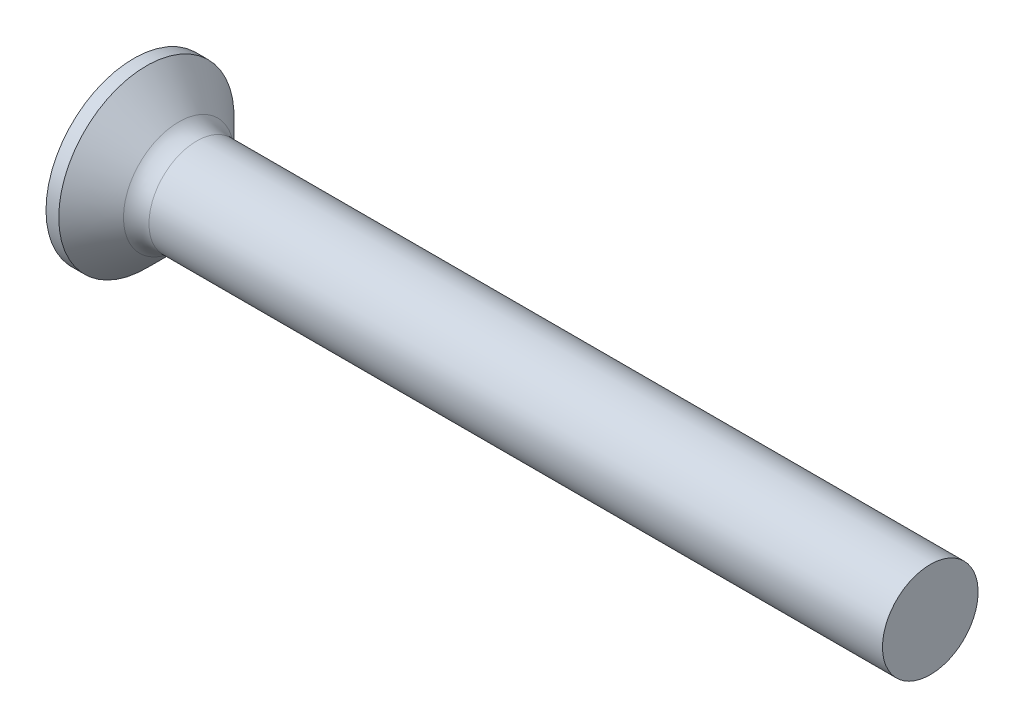
SolidWorks part; units mm, degrees
ref_plane "Plane1" through (0, 0, 0) normal (0, 0, 1) x (1, 0, 0)
ref_plane "Plane2" through (0, 0, 0) normal (0, 1, 0) x (1, 0, 0)
ref_plane "Plane3" through (0, 0, 0) normal (1, 0, 0) x (0, 0, -1)
sketch "BodySke" plane through (0, 0, 0) normal (0, 0, 1) x (1, 0, 0)
  line L0 (0, 0) -> (0, 2.75)
  line L1 (0, 2.75) -> (0.4, 2.75)
  line L2 (1.65, 1.5) -> (25, 1.5)
  line L3 (25, 1.5) -> (25, 0)
  line L4 (25, 0) -> (0, 0)
  line L5 (-6.35, 0) -> (82.55, 0) construction
  line L6 (1.65, -1.5) -> (25, -1.5) construction
  line L7 (0.4, -2.75) -> (1.65, -1.5) construction
  line L8 (0.4, 2.75) -> (1.65, 1.5)
  line L9 (0, -2.75) -> (0.4, -2.75) construction
  line L10 (2.15, 3.0875) -> (2.15, -6.4375) construction
  line L11 (0, 6.35) -> (0, -3.175) construction
  dimension "Diameter" = 3
  dimension "Length" = 25
  dimension "Head_ht" = 1.65
  dimension "Head_dia" = 5.5
  dimension "Head_ang" = 90
  dimension "D6" = 0.4
  dimension "Advance" = 0.5
  dimension "Thread_nom" = 25
revolve "Base-Revolve" add sketch "BodySke" angle 360 about L5
cosmetic thread "ThreadCosmetic" [suppressed] parameters "Thread_length"=22.85, "Thread_minor"=2.439
fillet "Fillet1" radius 0.8 1 edges at (1.65, 0, 1.5)
sketch "Sketch3" plane through (0, 0, 0) normal (-1, 0, 0) x (0, 0, 1)
  line L0 (-0.37, 1.5) -> (0.37, 1.5)
  line L1 (0.37, 1.5) -> (0.37, -1.5)
  line L2 (0.37, -1.5) -> (-0.37, -1.5)
  line L3 (-0.37, -1.5) -> (-0.37, 1.5)
  dimension "D1" = 1.5
  dimension "Cross_dia" = 3
  dimension "D2" = 0.37
  dimension "Cross_width" = 0.74
ref_plane "Plane4" through (2.01, 0, 0) normal (-1, 0, 0) x (0, 0, 1)
sketch "Sketch4" plane through (2.01, 0, 0) normal (-1, 0, 0) x (0, 0, 1)
  line L0 (-0.37, 0.4979) -> (0.37, 0.4979)
  line L3 (0.37, 0.4979) -> (0.37, -0.4979)
  line L4 (0.37, -0.4979) -> (-0.37, -0.4979)
  line L5 (-0.37, -0.4979) -> (-0.37, 0.4979)
  dimension "D1" = 0.74
  dimension "D2" = 0.9957
  dimension "D3" = 0.37
  dimension "D4" = 0.4979
loft "Recess" cut profiles "Sketch3", "Sketch4"
pattern_circular "RecPat" count 2 every 90 about axis through (0, 0, 0) along (1, 0, 0) of "Recess"
sketch "RecCorSke" plane through (0, 0, 0) normal (0, 0, 1) x (1, 0, 0)
  line L0 (-3.175, 0) -> (15.875, 0) construction
  line L2 (0, 0) -> (0, 0.6966)
  line L3 (0, 0.6966) -> (2.01, 0.556)
  line L4 (2.01, 0.556) -> (2.1907, 0)
  line L5 (2.1907, 0) -> (0, 0)
  dimension "Diameter" = 1.112
  dimension "Depth" = 2.01
  dimension "Draft_angle" = 4
  dimension "Bottom_angle" = 18
revolve "RecessCore" cut sketch "RecCorSke" angle 360 about L0
sketch "ThdSchSke" plane through (0, 0, 0) normal (0, 0, 1) x (1, 0, 0)
  line L0 (2.15, -1.2195) -> (1.9536, -1.5)
  line L1 (2.15, -1.2195) -> (2.3464, -1.5)
  line L2 (2.3464, -1.5) -> (2.3464, -1.875)
  line L3 (-3.175, 0) -> (5.1513, 0) construction
  line L5 (2.3464, -1.875) -> (1.9536, -1.875)
  line L6 (1.9536, -1.875) -> (1.9536, -1.5)
  line L7 (0, 2.75) -> (0, -2.75) construction
  dimension "Thread_minor" = 2.439
  dimension "Diameter" = 3
  dimension "Start" = 2.15
  dimension "SideAngle" = 55
  dimension "VeeAngle" = 70
  dimension "Overcut" = 3.75
revolve "ThreadSchematic" [suppressed] cut sketch "ThdSchSke" angle 360 about L3
pattern_linear "ThdSchPat" [suppressed]
equation "\"D1@Sketch3\" = \"Cross_dia@Sketch3\" / 2"
equation "\"D2@Sketch3\" = \"Cross_width@Sketch3\" / 2"
equation "\"Depth@RecCorSke\" = \"Cross_depth@Plane4\""
equation "\"D1@Sketch4\" = \"Cross_width@Sketch3\""
equation "\"D2@Sketch4\" = \"Cross_dia@Sketch3\" - 2.0 * \"Cross_depth@Plane4\" * tan(26.5  * 0.017453292)"
equation "\"D3@Sketch4\" = \"D1@Sketch4\" / 2"
equation "\"D4@Sketch4\" = \"D2@Sketch4\" / 2"
equation "\"Thread_length@ThreadCosmetic\" = ((sgn( (\"Length@BodySke\" - \"Advance@BodySke\" * 1.0 - \"Head_ht@BodySke\" ) - \"Thread_nom@BodySke\" )-1)*( (\"Length@BodySke\" - \"Advance@BodySke\" * 1.0 - \"Head_ht@BodySke\" ) - \"Thread_nom@BodySke\" ))/-2+ \"Thread_nom@BodySke\""
equation "\"Thread_minor@ThdSchSke\" = \"Thread_minor@ThreadCosmetic\""
equation "\"Diameter@ThdSchSke\" = \"Diameter@BodySke\""
equation "\"Overcut@ThdSchSke\" = \"Diameter@BodySke\" * 1.25"
equation "\"Start@ThdSchSke\" = 0.000001 + \"Length@BodySke\" - \"Thread_length@ThreadCosmetic\"  '---Countersunk---"
equation "\"Num_threads@ThdSchPat\" = int( \"Thread_length@ThreadCosmetic\" / \"Advance@BodySke\" + 0.999 )  + 1"
equation "\"Advance@ThdSchPat\" = \"Thread_length@ThreadCosmetic\" /  (\"Num_threads@ThdSchPat\" - 1) 'relax it"
